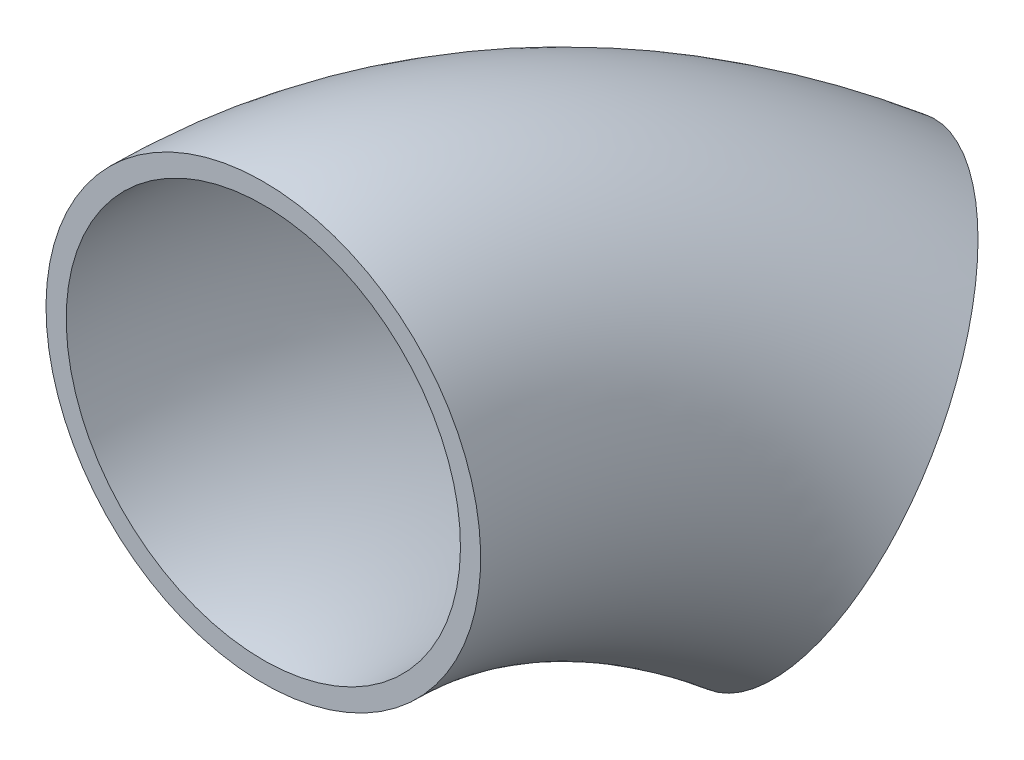
SolidWorks part; units mm, degrees
ref_plane "Front" through (0, 0, 0) normal (0, 0, 1) x (1, 0, 0)
ref_plane "Top" through (0, 0, 0) normal (0, 1, 0) x (1, 0, 0)
ref_plane "Side" through (0, 0, 0) normal (1, 0, 0) x (0, 0, -1)
sketch "PipeSketch" plane through (0, 0, 0) normal (0, 0, 1) x (1, 0, 0)
  circle A0 centre (0, 0) radius 136.525
  circle A1 centre (0, 0) radius 123.825
  dimension "OuterDiameter" = 273.05
  dimension "InnerDiameter" = 247.65
sketch "FilterSketch" plane through (0, 0, 0) normal (0, 0, 1) x (1, 0, 0)
  circle A0 centre (0, 0) radius 127 construction
  dimension "NominalDiameter" = 254
sketch3d "3DSketch1"
  arc A0 (0, 0, 0) -> (78.9077, -78.9077, -269.4077) centre (269.4077, -269.4077, 0) ccw construction
  arc A1 (0, 0, 0) -> (78.9077, -78.9077, -269.4077) centre (269.4077, -269.4077, 0) ccw
  point P3 (0, -538.8154, 0)
  point P4 (0, -538.8154, 0)
sweep "Sweep1" add profiles "PipeSketch" path "3DSketch1"
